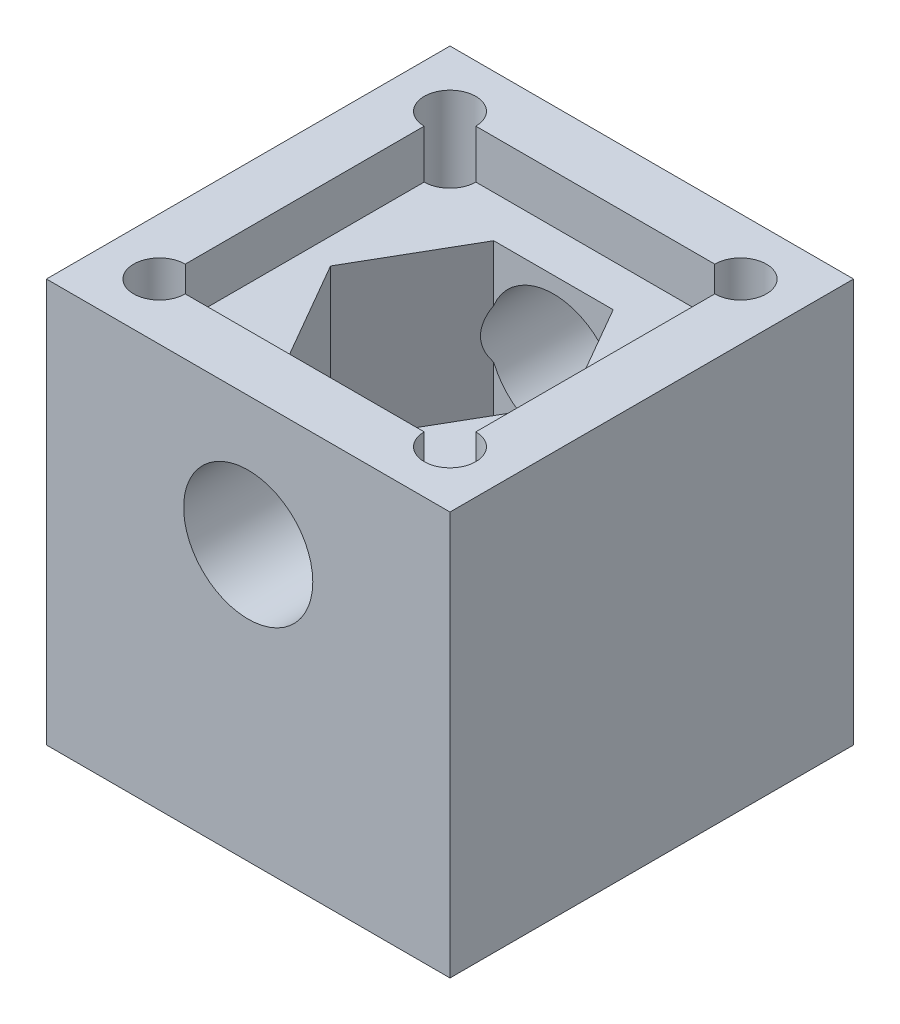
SolidWorks part; units mm, degrees
ref_plane "Спереди" through (0, 0, 0) normal (0, 0, 1) x (1, 0, 0)
ref_plane "Сверху" through (0, 0, 0) normal (0, 1, 0) x (1, 0, 0)
ref_plane "Справа" through (0, 0, 0) normal (1, 0, 0) x (0, 0, -1)
sketch "Sketch1" plane through (0, 0, 0) normal (0, 1, 0) x (1, 0, 0)
  line L1 (12.5, -12.5) -> (-12.5, -12.5)
  line L2 (12.5, -12.5) -> (12.5, 12.5)
  line L3 (12.5, 12.5) -> (-12.5, 12.5)
  line L4 (-12.5, -12.5) -> (-12.5, 12.5)
  line L5 (12.5, -12.5) -> (-12.5, 12.5) construction
  line L6 (12.5, 12.5) -> (-12.5, -12.5) construction
  point P0 (0, 0)
  dimension "D1" = 25
extrude "Boss-Extrude1" add sketch "Sketch1" along normal blind 25
sketch "Sketch2" plane through (0, 0, 12.5) normal (0, 0, 1) x (1, 0, 0)
  line L0 (-12.5, 17) -> (12.5, 17) construction
  line L1 (-12.5, 25) -> (-12.5, 0) construction
  line L2 (12.5, 25) -> (12.5, 0) construction
  line L3 (-12.5, 25) -> (12.5, 25) construction
  circle A0 centre (0, 17) radius 4
  dimension "D1" = 8
  dimension "D2" = 8
extrude "Cut-Extrude1" cut sketch "Sketch2" against normal through all
sketch "Sketch4" plane through (0, 25, 0) normal (0, 1, 0) x (1, 0, 0)
  circle A0 centre (0, 0) radius 4.15
  dimension "D1" = 8.3
extrude "Cut-Extrude2" cut sketch "Sketch4" against normal through all
sketch "Sketch5" plane through (0, 25, 0) normal (0, 1, 0) x (1, 0, 0)
  line L1 (-3.7, -6.4086) -> (3.7, -6.4086)
  line L2 (3.7, -6.4086) -> (7.4, 0)
  line L3 (7.4, 0) -> (3.7, 6.4086)
  line L4 (3.7, 6.4086) -> (-3.7, 6.4086)
  line L5 (-3.7, 6.4086) -> (-7.4, 0)
  line L6 (-7.4, 0) -> (-3.7, -6.4086)
  line L7 (-12.5, -12.5) -> (12.5, -12.5) construction
  circle A0 centre (0, 0) radius 7.4 construction
  dimension "D1" = 14.8
extrude "Cut-Extrude3" cut sketch "Sketch5" against normal blind 18
sketch "Sketch6" plane through (0, 25, 0) normal (0, 1, 0) x (1, 0, 0)
  line L1 (-9, 9) -> (9, 9) construction
  line L2 (-9, 9) -> (-9, -9) construction
  line L3 (-9, -9) -> (9, -9) construction
  line L4 (9, 9) -> (9, -9) construction
  line L5 (-9, 9) -> (9, -9) construction
  line L6 (-9, -9) -> (9, 9) construction
  circle A0 centre (9, -9) radius 1.6
  circle A1 centre (-9, -9) radius 1.6
  circle A2 centre (-9, 9) radius 1.6
  circle A3 centre (9, 9) radius 1.6
  point P0 (0, 0)
  dimension "D1" = 3.2
  dimension "D2" = 18
extrude "Cut-Extrude4" cut sketch "Sketch6" against normal through all
sketch "Sketch7" plane through (0, 25, 0) normal (0, 1, 0) x (1, 0, 0)
  line L1 (-9, 9) -> (9, 9)
  line L2 (-9, 9) -> (-9, -9)
  line L3 (-9, -9) -> (9, -9)
  line L4 (9, 9) -> (9, -9)
  line L5 (-9, 9) -> (9, -9) construction
  line L6 (-9, -9) -> (9, 9) construction
  point P0 (0, 0)
  dimension "D1" = 18
extrude "Cut-Extrude5" cut sketch "Sketch7" against normal blind 3
